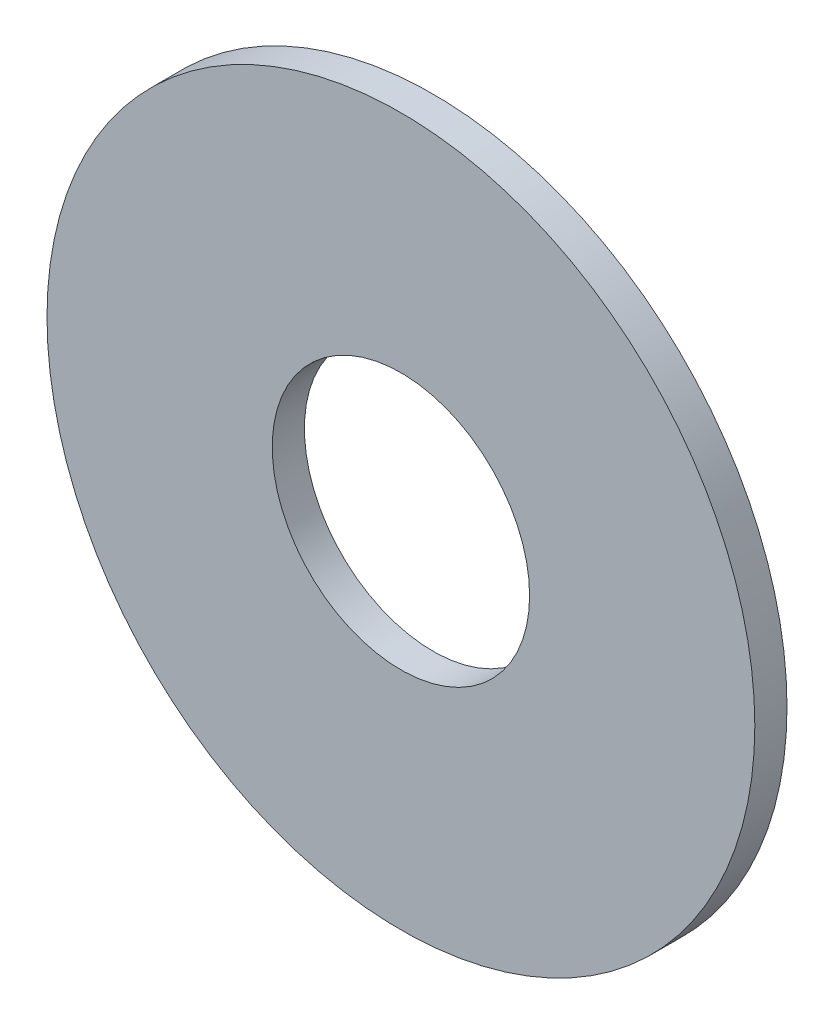
SolidWorks part; units mm, degrees
material "Alliage 7079"
ref_plane "Face" through (0, 0, 0) normal (0, 0, 1) x (1, 0, 0)
ref_plane "Dessus" through (0, 0, 0) normal (0, 1, 0) x (1, 0, 0)
ref_plane "Droite" through (0, 0, 0) normal (1, 0, 0) x (0, 0, -1)
sketch "Esquisse1" plane through (0, 0, 0) normal (0, 0, 1) x (1, 0, 0)
  circle A0 centre (0, 0) radius 5.5
  circle A1 centre (0, 0) radius 2
  dimension "D1" = 4
  dimension "D2" = 11
extrude "Extrusion1" add sketch "Esquisse1" along normal blind 0.5
